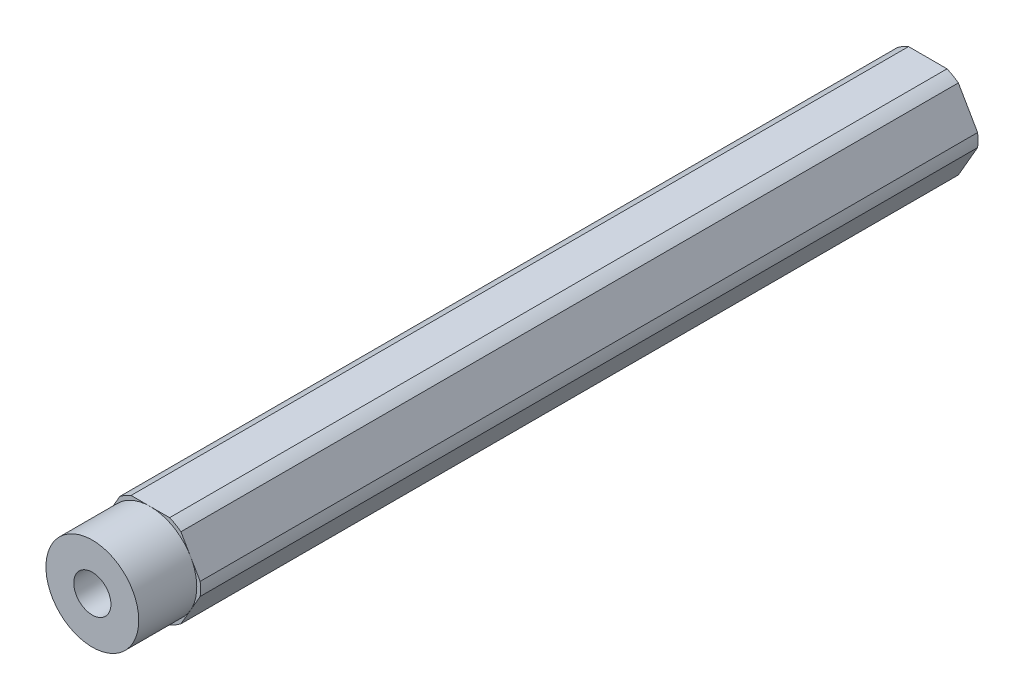
SolidWorks part; units mm, degrees
material "7075-T6 (SN)"
ref_plane "Front Plane" through (0, 0, 0) normal (0, 0, 1) x (1, 0, 0)
ref_plane "Top Plane" through (0, 0, 0) normal (0, 1, 0) x (1, 0, 0)
ref_plane "Right Plane" through (0, 0, 0) normal (1, 0, 0) x (0, 0, -1)
sketch "Sketch1" plane through (0, 0, 0) normal (0, 0, 1) x (1, 0, 0)
  line L1 (4.1818, -5.457) -> (6.8168, -0.893)
  line L2 (6.8168, 0.893) -> (4.1818, 5.457)
  line L3 (2.635, 6.35) -> (-2.635, 6.35)
  line L4 (-4.1818, 5.457) -> (-6.8168, 0.893)
  line L5 (-6.8168, -0.893) -> (-4.1818, -5.457)
  line L6 (-2.635, -6.35) -> (2.635, -6.35)
  circle A0 centre (0, 0) radius 6.35 construction
  arc A1 (-6.8168, 0.893) -> (-6.8168, -0.893) centre (0, 0) ccw
  arc A2 (-2.635, 6.35) -> (-4.1818, 5.457) centre (0, 0) ccw
  arc A3 (4.1818, 5.457) -> (2.635, 6.35) centre (0, 0) ccw
  arc A4 (6.8168, -0.893) -> (6.8168, 0.893) centre (0, 0) ccw
  arc A5 (2.635, -6.35) -> (4.1818, -5.457) centre (0, 0) ccw
  arc A6 (-4.1818, -5.457) -> (-2.635, -6.35) centre (0, 0) ccw
  circle A7 centre (0, 0) radius 2.54
  dimension "D2" = 13.75
  dimension "D3" = 5.08
  dimension "D1" = 12.7
extrude "Boss-Extrude1" add sketch "Sketch1" along normal blind 114.3
sketch "Sketch2" plane through (0, 0, 114.3) normal (0, 0, 1) x (1, 0, 0)
  circle A0 centre (0, 0) radius 6.35
  dimension "D1" = 12.7
extrude "Cut-Extrude1" cut sketch "Sketch2" against normal blind 7.9375 flip side to cut
